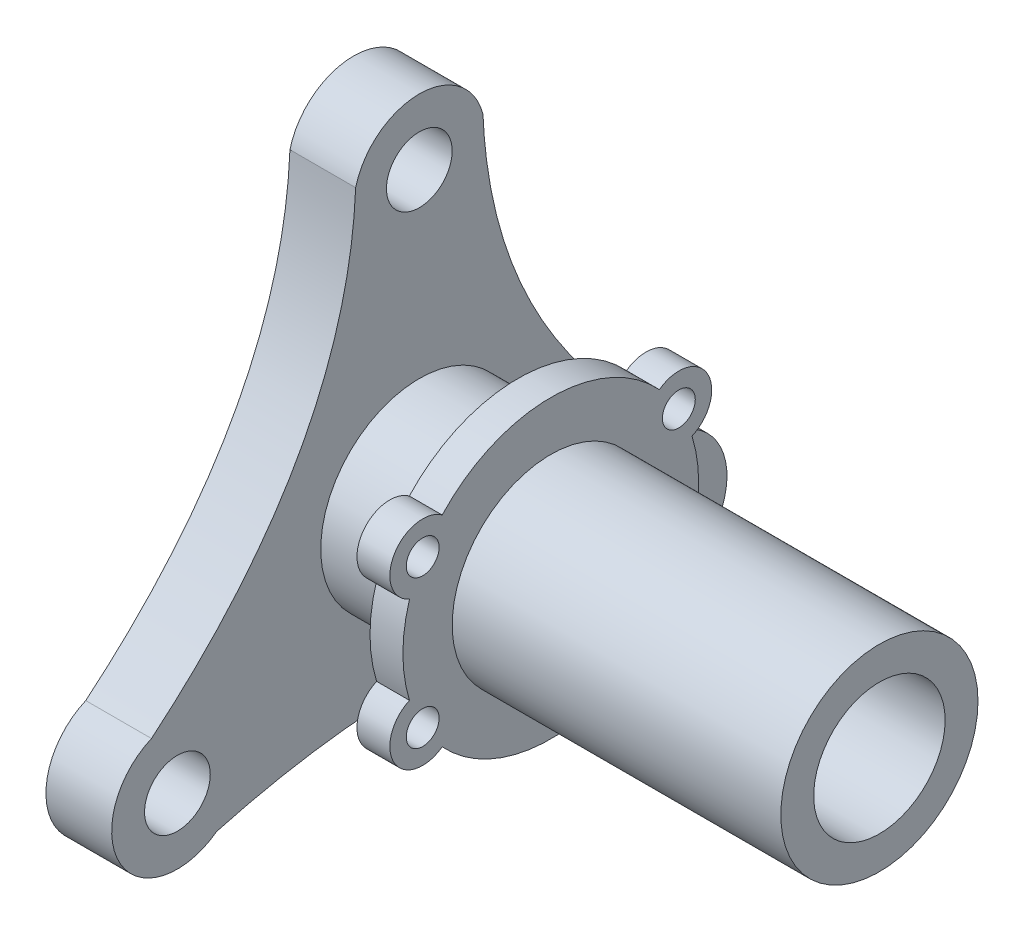
SolidWorks part; units mm, degrees
material "6063-T6"
ref_plane "Front Plane" through (0, 0, 0) normal (0, 0, 1) x (1, 0, 0)
ref_plane "Top Plane" through (0, 0, 0) normal (0, 1, 0) x (1, 0, 0)
ref_plane "Right Plane" through (0, 0, 0) normal (1, 0, 0) x (0, 0, -1)
sketch "Sketch2" plane through (0, 0, 0) normal (1, 0, 0) x (0, 0, -1)
  circle A1 centre (0, 42.5) radius 5
  arc A2 (9.6848, 44.9908) -> (-9.6848, 44.9908) centre (0, 42.5) ccw
  arc A3 (30.8219, -29.2619) -> (40.7525, -12.0617) centre (36.8061, -21.25) ccw
  circle A4 centre (36.8061, -21.25) radius 5
  arc A5 (-40.7525, -12.0617) -> (-30.8219, -29.2619) centre (-36.8061, -21.25) ccw
  circle A6 centre (-36.8061, -21.25) radius 5
  circle A7 centre (0, 0) radius 10
  spline S0 degree 3 poles (-40.7525, -12.0617) (-20.9349, 4.4206) (-10.579, 23.4381) (-9.6848, 44.9908) knots 0 0 0 0 0.868352 0.868352 0.868352 0.868352
  spline S1 degree 2 poles (40.7525, -12.0617) (11.0723, 12.1621) (9.6848, 44.9908) knots 0 0 0 1 1 1
  spline S2 degree 2 poles (-30.8219, -29.2619) (1.4261, -20.4459) (30.8219, -29.2619) knots 0 0 0 0.9072 0.9072 0.9072
  point P16 (0, 0)
  dimension "D1" = 36.8061
  dimension "D2" = 20
  dimension "D3" = 10
  dimension "D6" = 67.0641
  dimension "D7" = 62.4754
  dimension "D8" = 67.0114
  dimension "D9" = 53.3852
  dimension "D16" = 20
  dimension "D5" = 63.75
  dimension "D10" = 53.3852
  dimension "D11" = 57.0525
  dimension "D12" = 64.9629
  dimension "D13" = 57.0525
  dimension "D14" = 64.9629
  dimension "D15" = 61.6439
  dimension "D4" = 3
extrude "Boss-Extrude2" add sketch "Sketch2" along normal blind 10
sketch "Sketch3" plane through (10, 0, 0) normal (1, 0, 0) x (0, 0, -1)
  circle A0 centre (0, 0) radius 15
  circle A1 centre (0, 0) radius 10 construction
  circle A2 centre (0, 0) radius 10
  dimension "D1" = 30
extrude "Boss-Extrude3" add sketch "Sketch3" along normal blind 20
sketch "Sketch4" plane through (30, 0, 0) normal (1, 0, 0) x (0, 0, -1)
  circle A3 centre (19.4856, 11.25) radius 2.5
  arc A4 (21.489, 6.6689) -> (16.5199, 15.2755) centre (19.4856, 11.25) ccw
  circle A5 centre (19.4856, -11.25) radius 2.5
  arc A6 (16.5199, -15.2755) -> (21.489, -6.6689) centre (19.4856, -11.25) ccw
  circle A9 centre (-19.4856, -11.25) radius 2.5
  arc A10 (-21.489, -6.6689) -> (-16.5199, -15.2755) centre (-19.4856, -11.25) ccw
  circle A11 centre (-19.4856, 11.25) radius 2.5
  arc A12 (-16.5199, 15.2755) -> (-21.489, 6.6689) centre (-19.4856, 11.25) ccw
  arc A13 (-16.5199, -15.2755) -> (16.5199, -15.2755) centre (0, 0) ccw
  arc A14 (16.5199, 15.2755) -> (-16.5199, 15.2755) centre (0, 0) ccw
  arc A15 (-21.489, 6.6689) -> (-21.489, -6.6689) centre (0, 0) ccw
  arc A16 (21.489, -6.6689) -> (21.489, 6.6689) centre (0, 0) ccw
  circle A17 centre (0, 0) radius 15 construction
  circle A18 centre (0, 0) radius 15
  point P23 (0, 0)
  dimension "D2" = 5
  dimension "D3" = 10
extrude "Boss-Extrude5" add sketch "Sketch4" against normal blind 5
sketch "Sketch5" plane through (30, 0, 0) normal (1, 0, 0) x (0, 0, -1)
  circle A0 centre (0, 0) radius 15
  circle A1 centre (0, 0) radius 10 construction
  circle A2 centre (0, 0) radius 10
  dimension "D1" = 30
extrude "Boss-Extrude6" add sketch "Sketch5" along normal blind 50
